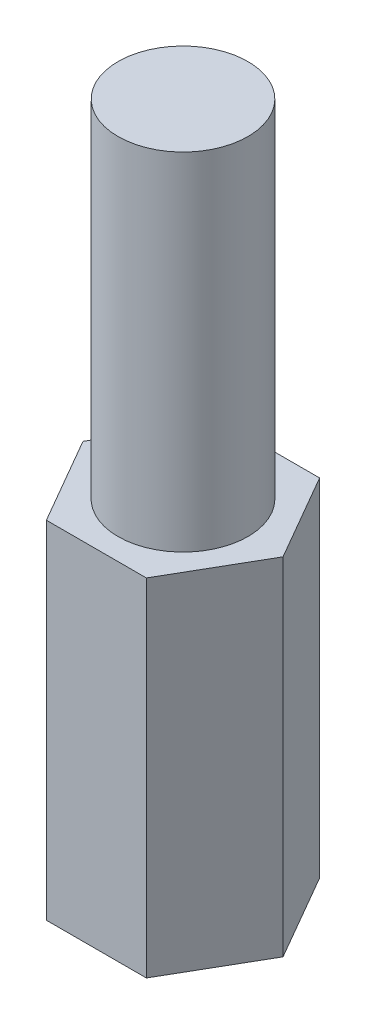
SolidWorks part; units mm, degrees
ref_plane "前视基准面" through (0, 0, 0) normal (0, 0, 1) x (1, 0, 0)
ref_plane "上视基准面" through (0, 0, 0) normal (0, 1, 0) x (1, 0, 0)
ref_plane "右视基准面" through (0, 0, 0) normal (1, 0, 0) x (0, 0, -1)
sketch "草图1" plane through (0, 0, 0) normal (0, 1, 0) x (1, 0, 0)
  line L1 (-1.1547, -2) -> (1.1547, -2)
  line L2 (1.1547, -2) -> (2.3094, 0)
  line L3 (2.3094, 0) -> (1.1547, 2)
  line L4 (1.1547, 2) -> (-1.1547, 2)
  line L5 (-1.1547, 2) -> (-2.3094, 0)
  line L6 (-2.3094, 0) -> (-1.1547, -2)
  circle A0 centre (0, 0) radius 2 construction
  dimension "D1" = 4
extrude "凸台-拉伸1" add sketch "草图1" along normal blind 8
sketch "草图2" plane through (0, 8, 0) normal (0, 1, 0) x (1, 0, 0)
  circle A0 centre (0, 0) radius 1.5
  dimension "D1" = 3
extrude "凸台-拉伸2" add sketch "草图2" along normal blind 8
sketch "草图3" plane through (0, 0, 0) normal (0, -1, 0) x (1, 0, 0)
  circle A0 centre (0, 0) radius 1.5
  dimension "D1" = 3
extrude "切除-拉伸1" cut sketch "草图3" against normal blind 5
